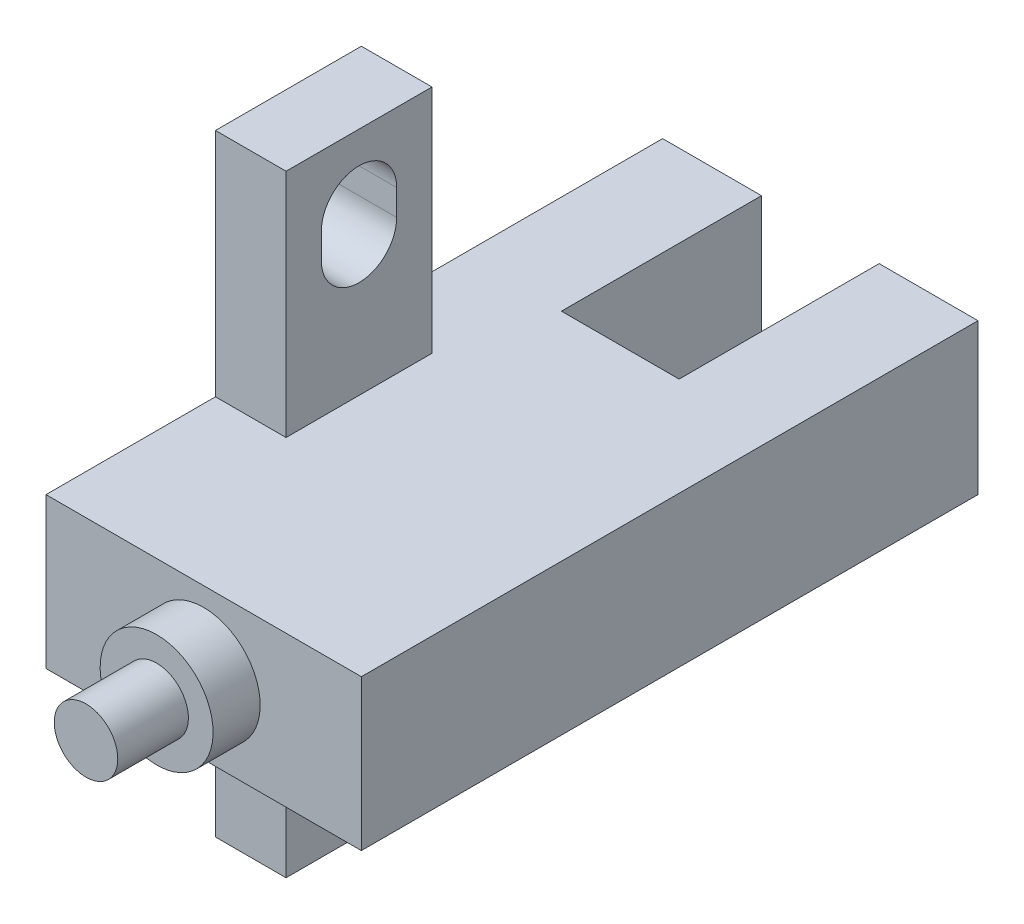
SolidWorks part; units mm, degrees
ref_plane "Front" through (0, 0, 0) normal (0, 0, 1) x (1, 0, 0)
ref_plane "Top" through (0, 0, 0) normal (0, 1, 0) x (1, 0, 0)
ref_plane "Right" through (0, 0, 0) normal (1, 0, 0) x (0, 0, -1)
sketch "Sketch1" plane through (0, 0, 0) normal (0, 1, 0) x (1, 0, 0)
  line L0 (0, -2.1658) -> (0, 28.3074) construction
  line L1 (-6.7, 0) -> (6.7, 0)
  line L2 (-6.7, 0) -> (-6.7, 26.2)
  line L3 (-6.7, 26.2) -> (6.7, 26.2)
  line L4 (6.7, 0) -> (6.7, 26.2)
  dimension "D1" = 26.2
  dimension "D2" = 13.4
extrude "Boss-Extrude1" add sketch "Sketch1" along normal blind 6.4
sketch "Sketch2" plane through (0, 6.4, 0) normal (0, 1, 0) x (1, 0, 0)
  line L0 (0, -2.251) -> (0, 27.6006) construction
  line L1 (6.7, 26.2) -> (-6.7, 26.2) construction
  line L2 (-2.5, 26.2) -> (2.5, 26.2)
  line L3 (-2.5, 26.2) -> (-2.5, 17.7)
  line L4 (-2.5, 17.7) -> (2.5, 17.7)
  line L5 (2.5, 26.2) -> (2.5, 17.7)
  dimension "D1" = 5
  dimension "D2" = 8.5
extrude "Cut-Extrude1" cut sketch "Sketch2" against normal blind 6.4
sketch "Sketch3" plane through (-6.7, 0, 0) normal (-1, 0, 0) x (0, 0, 1)
  line L0 (1.4491, 3.2) -> (-28.224, 3.2) construction
  line L1 (-13.4, 16.2) -> (-7.2, 16.2)
  line L2 (-13.4, 16.2) -> (-13.4, -9.8)
  line L3 (-13.4, -9.8) -> (-7.2, -9.8)
  line L4 (-7.2, 16.2) -> (-7.2, -9.8)
  line L5 (-26.2, 6.4) -> (0, 6.4) construction
  line L6 (-26.2, 0) -> (0, 0) construction
  line L7 (-10.3, -10.7561) -> (-10.3, 17.6625) construction
  line L8 (0, 6.4) -> (0, 0) construction
  dimension "D1" = 26
  dimension "D2" = 6.2
  dimension "D3" = 10.3
extrude "Boss-Extrude2" add sketch "Sketch3" against normal blind 3
sketch "Sketch4" plane through (-3.7, 0, 0) normal (1, 0, 0) x (0, 0, -1)
  line L0 (10.3, 13.25) -> (10.3, 12.15) construction
  line L1 (11.9, 13.25) -> (11.9, 12.15)
  line L2 (8.7, 13.25) -> (8.7, 12.15)
  line L3 (-1.3286, 3.2) -> (27.203, 3.2) construction
  line L4 (0, 6.4) -> (26.2, 6.4) construction
  line L5 (0, 0) -> (26.2, 0) construction
  line L6 (10.3, -6.85) -> (10.3, -5.75) construction
  line L7 (11.9, -6.85) -> (11.9, -5.75)
  line L8 (8.7, -6.85) -> (8.7, -5.75)
  line L9 (0, 6.4) -> (0, 0) construction
  arc A0 (11.9, 13.25) -> (8.7, 13.25) centre (10.3, 13.25) ccw
  arc A1 (8.7, 12.15) -> (11.9, 12.15) centre (10.3, 12.15) ccw
  arc A2 (11.9, -6.85) -> (8.7, -6.85) centre (10.3, -6.85) cw
  arc A3 (8.7, -5.75) -> (11.9, -5.75) centre (10.3, -5.75) cw
  point P2 (10.3, 12.7)
  point P15 (10.3, -6.3)
  dimension "D2" = 3.2
  dimension "D4" = 4.3
  dimension "D1" = 10.3
  dimension "D3" = 19
extrude "Cut-Extrude2" cut sketch "Sketch4" against normal through all
ref_plane "Plane1" through (0, 0, 0) normal (1, 0, 0) x (0, 0, -1)
sketch "Sketch5" plane through (0, 0, 0) normal (1, 0, 0) x (0, 0, -1)
  line L0 (27.3545, 3.2) -> (-6.2605, 3.2) construction
  line L1 (0, 6.4) -> (26.2, 6.4) construction
  line L2 (0, 0) -> (26.2, 0) construction
  line L3 (0, 3.2) -> (0, 5.6)
  line L4 (0, 5.6) -> (-2, 5.6)
  line L5 (-2, 5.6) -> (-2, 4.55)
  line L6 (-2, 4.55) -> (-5, 4.55)
  line L7 (-5, 4.55) -> (-5, 3.2)
  line L8 (0, 6.4) -> (0, 0) construction
  line L9 (-5, 3.2) -> (0, 3.2)
  dimension "D1" = 4.8
  dimension "D2" = 2
  dimension "D3" = 2.7
  dimension "D4" = 5
revolve "Revolve1" add sketch "Sketch5" angle 360 about L0
